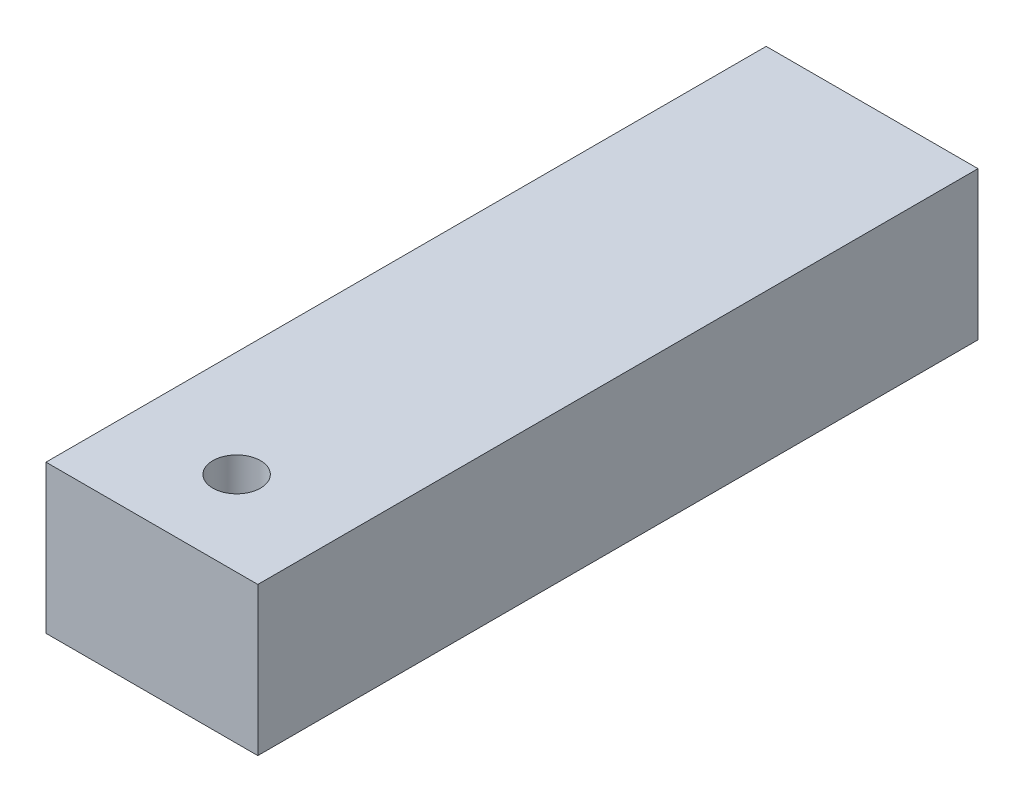
SolidWorks part; units mm, degrees
ref_plane "Ebene vorne" through (0, 0, 0) normal (0, 0, 1) x (1, 0, 0)
ref_plane "Ebene oben" through (0, 0, 0) normal (0, 1, 0) x (1, 0, 0)
ref_plane "Ebene rechts" through (0, 0, 0) normal (1, 0, 0) x (0, 0, -1)
sketch "Skizze1" plane through (0, 0, 0) normal (0, 0, 1) x (1, 0, 0)
  line L0 (-25, 17.5) -> (25, -17.5) construction
  line L1 (-25, 17.5) -> (25, 17.5)
  line L2 (-25, 17.5) -> (-25, -17.5)
  line L3 (-25, -17.5) -> (25, -17.5)
  line L4 (25, 17.5) -> (25, -17.5)
  dimension "D1" = 35
  dimension "D2" = 50
extrude "Linear austragen1" add sketch "Skizze1" along normal blind 170
sketch "Skizze2" plane through (0, 17.5, 0) normal (0, 1, 0) x (1, 0, 0)
  line L0 (25, 0) -> (-25, 0) construction
  circle A0 centre (0, -150) radius 5.6348
  dimension "D1" = 150
extrude "Linear austragen2" cut sketch "Skizze2" against normal through all
